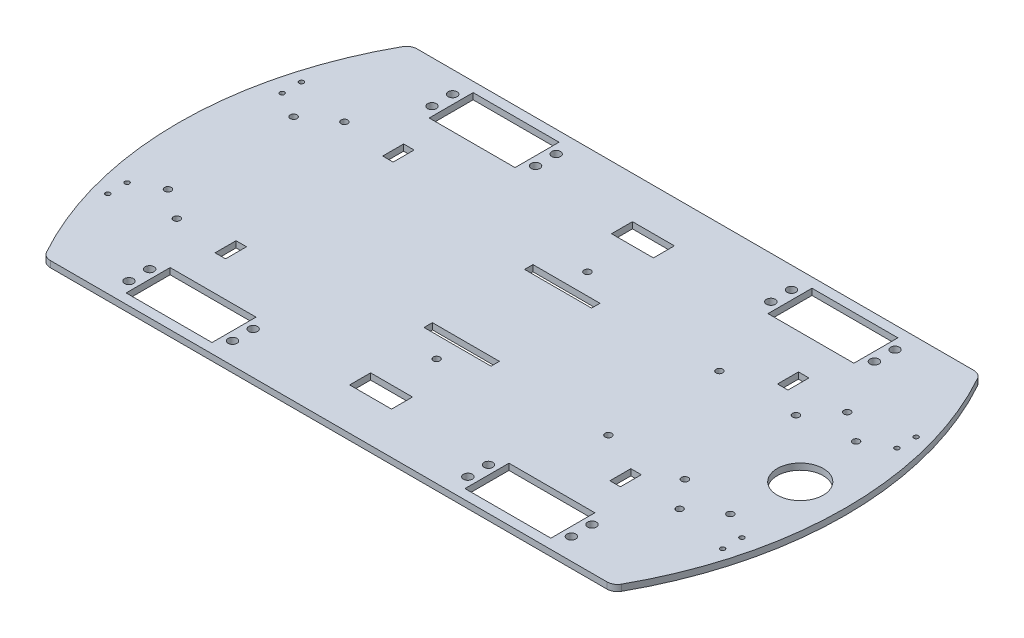
SolidWorks part; units mm, degrees
material "Acrylic (Medium-high impact)"
ref_plane "Front Plane" through (0, 0, 0) normal (0, 0, 1) x (1, 0, 0)
ref_plane "Top Plane" through (0, 0, 0) normal (0, 1, 0) x (1, 0, 0)
ref_plane "Right Plane" through (0, 0, 0) normal (1, 0, 0) x (0, 0, -1)
sketch "Sketch1" plane through (0, 0, 0) normal (0, 1, 0) x (1, 0, 0)
  line L1 (-150, -87.5) -> (150, -87.5) construction
  line L2 (-150, -87.5) -> (-150, 87.5) construction
  line L3 (-150, 87.5) -> (150, 87.5) construction
  line L4 (150, -87.5) -> (150, 87.5) construction
  line L5 (-150, -87.5) -> (150, 87.5) construction
  line L6 (-150, 87.5) -> (150, -87.5) construction
  line L7 (-94.037, 37.4826) -> (-29.037, 37.4826) construction
  line L12 (-150, 0) -> (150, 0) construction
  line L13 (-126.5544, 87.5) -> (-104.0544, 87.5)
  line L19 (-89.087, -10.5) -> (-48.087, 10.5) construction
  line L20 (-89.087, 10.5) -> (-48.087, -10.5) construction
  line L24 (-94.037, -37.4826) -> (-29.037, -37.4826) construction
  line L26 (-61.537, 37.4826) -> (-61.537, -37.4826) construction
  line L27 (-68.587, 10.5) -> (-68.587, -10.5) construction
  line L45 (80, 57.5) -> (80, -57.5) construction
  line L47 (40.8363, 87.5) -> (-18.2182, 87.5)
  line L67 (-126.5544, -87.5) -> (-104.0544, -87.5)
  line L78 (40.8363, -87.5) -> (-18.2182, -87.5)
  line L79 (120.8363, -87.5) -> (137.7923, -87.5)
  line L80 (120.8363, 87.5) -> (137.7923, 87.5)
  line L81 (54.4, -34.9) -> (64.4, -37.9) construction
  line L82 (54.4, 37.9) -> (64.4, 37.9) construction
  line L83 (54.4, 37.9) -> (54.4, 34.9) construction
  line L84 (54.4, 34.9) -> (64.4, 34.9) construction
  line L85 (64.4, 37.9) -> (64.4, 34.9) construction
  line L86 (54.4, 37.9) -> (64.4, 34.9) construction
  line L87 (54.4, 34.9) -> (64.4, 37.9) construction
  line L88 (54.4, -37.9) -> (64.4, -34.9) construction
  line L89 (64.4, -37.9) -> (64.4, -34.9) construction
  line L90 (54.4, -34.9) -> (64.4, -34.9) construction
  line L91 (54.4, -37.9) -> (54.4, -34.9) construction
  line L92 (54.4, -37.9) -> (64.4, -37.9) construction
  line L93 (0, 87.5) -> (0, -87.5) construction
  line L94 (-6.77, -22) -> (25.23, -26) construction
  line L95 (127.5, -12.5) -> (137.5, -12.5) construction
  line L96 (127.5, -12.5) -> (127.5, 12.5) construction
  line L97 (127.5, 12.5) -> (137.5, 12.5) construction
  line L98 (137.5, -12.5) -> (137.5, 12.5) construction
  line L99 (127.5, -12.5) -> (137.5, 12.5) construction
  line L100 (127.5, 12.5) -> (137.5, -12.5) construction
  line L101 (-6.77, 22) -> (25.23, 22)
  line L102 (-6.77, 22) -> (-6.77, 26)
  line L103 (-6.77, 26) -> (25.23, 26)
  line L104 (25.23, 22) -> (25.23, 26)
  line L105 (-6.77, 22) -> (25.23, 26) construction
  line L106 (-6.77, 26) -> (25.23, 22) construction
  line L107 (-6.77, -26) -> (25.23, -22) construction
  line L108 (-6.77, -26) -> (25.23, -26)
  line L109 (25.23, -22) -> (25.23, -26)
  line L110 (-6.77, -22) -> (25.23, -22)
  line L111 (-6.77, -22) -> (-6.77, -26)
  line L112 (-0.77, -67.5) -> (19.23, -57.5) construction
  line L117 (-0.77, 57.5) -> (19.23, 57.5)
  line L118 (-0.77, 57.5) -> (-0.77, 67.5)
  line L119 (-0.77, 67.5) -> (19.23, 67.5)
  line L124 (19.23, 57.5) -> (19.23, 67.5)
  line L125 (-0.77, 57.5) -> (19.23, 67.5) construction
  line L126 (-0.77, 67.5) -> (19.23, 57.5) construction
  line L127 (-0.77, -57.5) -> (19.23, -67.5) construction
  line L128 (-0.77, -67.5) -> (19.23, -67.5)
  line L129 (19.23, -57.5) -> (19.23, -67.5)
  line L130 (-0.77, -57.5) -> (19.23, -57.5)
  line L131 (-0.77, -57.5) -> (-0.77, -67.5)
  line L132 (-104.0544, -87.5) -> (-18.2182, -87.5)
  line L133 (-127.5, -5) -> (-122.5, -5) construction
  line L134 (-127.5, -5) -> (-127.5, 5) construction
  line L135 (-127.5, 5) -> (-122.5, 5) construction
  line L136 (-122.5, -5) -> (-122.5, 5) construction
  line L137 (-127.5, -5) -> (-122.5, 5) construction
  line L138 (-127.5, 5) -> (-122.5, -5) construction
  line L140 (-104.0544, 87.5) -> (-18.2182, 87.5)
  line L141 (40.8363, -87.5) -> (120.8363, -87.5)
  line L142 (40.8363, 87.5) -> (120.8363, 87.5)
  line L143 (-61.537, -72.32) -> (-39.9764, -72.32) construction
  line L144 (80, -72.32) -> (50.3837, -72.32) construction
  line L145 (9.23, 98.8163) -> (9.23, -100.4279) construction
  line L146 (137.7923, 87.5) -> (145.0144, 87.5)
  line L147 (137.7923, -87.5) -> (145.0144, -87.5)
  line L148 (69.6, 82.82) -> (110.6, 82.82)
  line L149 (-71.937, -61.82) -> (-30.937, -61.82) construction
  line L150 (-71.937, -61.82) -> (-71.937, -82.82) construction
  line L151 (-71.937, -82.82) -> (-30.937, -82.82) construction
  line L152 (-30.937, -61.82) -> (-30.937, -82.82) construction
  line L153 (69.6, -61.82) -> (110.6, -61.82)
  line L154 (69.6, -61.82) -> (69.6, -82.82)
  line L155 (69.6, -82.82) -> (110.6, -82.82)
  line L156 (110.6, -61.82) -> (110.6, -82.82)
  line L157 (110.6, 61.82) -> (110.6, 82.82)
  line L158 (69.6, 61.82) -> (110.6, 61.82)
  line L159 (69.6, 61.82) -> (69.6, 82.82)
  line L160 (-71.937, 61.82) -> (-30.937, 61.82) construction
  line L161 (-30.937, 61.82) -> (-30.937, 82.82) construction
  line L162 (-71.937, 82.82) -> (-30.937, 82.82) construction
  line L163 (-71.937, 61.82) -> (-71.937, 82.82) construction
  line L164 (4.23, 35.4) -> (4.23, -35.9) construction
  line L165 (-120.7635, 13.4) -> (-39.9764, 13.4) construction
  line L166 (71.9375, 13.4) -> (158.7021, 13.4) construction
  line L167 (-363.8153, 13.4) -> (-363.8153, -13.4) construction
  line L168 (-363.8153, -13.4) -> (-440.2138, -13.4) construction
  line L169 (-440.2138, -13.4) -> (-440.2138, -35.4) construction
  line L170 (-440.2138, -35.4) -> (-480.6138, 5) construction
  line L171 (-480.6138, 5) -> (-440.2138, 45.4) construction
  line L172 (-440.2138, 45.4) -> (-440.2138, 13.4) construction
  line L173 (-440.2138, 13.4) -> (-363.8153, 13.4) construction
  line L174 (-92.137, 61.82) -> (-92.137, 82.82)
  line L175 (-92.137, -61.82) -> (-51.137, -61.82)
  line L176 (-92.137, -61.82) -> (-92.137, -82.82)
  line L177 (-92.137, -82.82) -> (-51.137, -82.82)
  line L178 (-51.137, -61.82) -> (-51.137, -82.82)
  line L179 (-92.137, 61.82) -> (-51.137, 61.82)
  line L180 (-92.137, 82.82) -> (-51.137, 82.82)
  line L181 (-51.137, 61.82) -> (-51.137, 82.82)
  line L182 (-82.5, 45) -> (-87.5, 45)
  line L183 (-82.5, -45) -> (-87.5, -45)
  line L184 (-82.5, -45) -> (-82.5, -35)
  line L185 (-82.5, -35) -> (-87.5, -35)
  line L186 (-87.5, -45) -> (-87.5, -35)
  line L187 (-82.5, -45) -> (-87.5, -35) construction
  line L188 (-82.5, -35) -> (-87.5, -45) construction
  line L189 (-82.5, 45) -> (-82.5, 35)
  line L190 (-82.5, 35) -> (-87.5, 35)
  line L191 (-87.5, 45) -> (-87.5, 35)
  line L192 (100.96, 35) -> (105.96, 35)
  line L193 (100.96, 45) -> (100.96, 35)
  line L194 (100.96, 45) -> (105.96, 45)
  line L195 (105.96, 45) -> (105.96, 35)
  line L196 (100.96, -45) -> (105.96, -45)
  line L197 (100.96, -45) -> (100.96, -35)
  line L198 (100.96, -35) -> (105.96, -35)
  line L199 (105.96, -45) -> (105.96, -35)
  line L201 (118.25, -26.5) -> (81.75, -26.5) construction
  line L202 (118.25, -26.5) -> (118.25, 26.5) construction
  line L203 (118.25, 26.5) -> (81.75, 26.5) construction
  line L204 (81.75, -26.5) -> (81.75, 26.5) construction
  line L205 (118.25, -26.5) -> (81.75, 26.5) construction
  line L206 (118.25, 26.5) -> (81.75, -26.5) construction
  arc A7 (-126.5544, 87.5) -> (-126.5544, -87.5) centre (25, 0) ccw
  circle A11 centre (-110.77, 40) radius 1.6
  circle A14 centre (-110.77, -40) radius 1.6
  circle A15 centre (-125, -30) radius 1.6
  circle A16 centre (9.23, -36) radius 1.6
  circle A17 centre (143.46, -30) radius 1.6
  circle A18 centre (143.46, 30) radius 1.6
  circle A19 centre (9.23, 36) radius 1.6
  circle A20 centre (-125, 30) radius 1.6
  circle A21 centre (-137.5, 37) radius 1.1
  circle A29 centre (-137.5, 46.2) radius 1.1
  circle A31 centre (-137.5, -37) radius 1.1
  circle A32 centre (-137.5, -46.2) radius 1.1
  circle A37 centre (-76.147, -77.245) radius 2.1 construction
  circle A38 centre (-76.147, -67.395) radius 2.1 construction
  circle A39 centre (-26.7247, -77.245) radius 2.1 construction
  circle A40 centre (-26.7247, -67.395) radius 2.1 construction
  circle A41 centre (-26.7247, 67.395) radius 2.1 construction
  circle A42 centre (-26.7247, 77.245) radius 2.1 construction
  circle A43 centre (-76.147, 67.395) radius 2.1 construction
  circle A44 centre (-76.147, 77.245) radius 2.1 construction
  circle A45 centre (65.39, -77.245) radius 2.1
  circle A46 centre (65.39, -67.395) radius 2.1
  circle A47 centre (114.8123, -77.245) radius 2.1
  circle A48 centre (114.8123, -67.395) radius 2.1
  circle A49 centre (114.8123, 67.395) radius 2.1
  circle A50 centre (114.8123, 77.245) radius 2.1
  circle A51 centre (65.39, 67.395) radius 2.1
  circle A52 centre (65.39, 77.245) radius 2.1
  arc A53 (145.0144, 87.5) -> (145.0144, -87.5) centre (-6.54, 0) cw
  circle A54 centre (155.96, 37) radius 1.1
  circle A55 centre (155.96, 46.2) radius 1.1
  circle A56 centre (155.96, -46.2) radius 1.1
  circle A57 centre (155.96, -37) radius 1.1
  circle A58 centre (-118.8, 13.4) radius 1.1 construction
  circle A59 centre (-60, 13.4) radius 1.1 construction
  circle A62 centre (-60, -13.4) radius 1.1 construction
  circle A63 centre (-118.8, -13.4) radius 1.1 construction
  circle A64 centre (94.66, 13.4) radius 1.1 construction
  circle A65 centre (153.46, 13.4) radius 1.1 construction
  circle A66 centre (153.46, -13.4) radius 1.1 construction
  circle A67 centre (94.66, -13.4) radius 1.1 construction
  circle A68 centre (-46.927, -67.395) radius 2.1
  circle A69 centre (-46.927, -77.245) radius 2.1
  circle A70 centre (-96.3493, -67.395) radius 2.1
  circle A71 centre (-96.3493, -77.245) radius 2.1
  circle A72 centre (-96.3493, 77.245) radius 2.1
  circle A73 centre (-96.3493, 67.395) radius 2.1
  circle A74 centre (-46.927, 77.245) radius 2.1
  circle A75 centre (-46.927, 67.395) radius 2.1
  circle A76 centre (129.23, 40) radius 1.6
  circle A77 centre (129.23, -40) radius 1.6
  circle A78 centre (-105, 0) radius 2.1 construction
  circle A79 centre (81.75, 26.5) radius 1.6
  circle A80 centre (146.828, 0) radius 11
  circle A81 centre (118.25, 26.5) radius 1.6
  circle A82 centre (81.75, -26.5) radius 1.6
  circle A83 centre (118.25, -26.5) radius 1.6
  point P0 (0, 0)
  point P18 (-68.587, 0)
  point P53 (59.4, 36.4)
  point P79 (59.4, -36.4)
  point P101 (9.23, 24)
  point P103 (132.5, 0)
  point P111 (9.23, -24)
  point P116 (9.23, 62.5)
  point P127 (9.23, -62.5)
  point P134 (-125, 0)
  point P145 (80, -72.32)
  point P153 (-61.537, -72.32)
  point P154 (80, 72.32)
  point P155 (-61.537, 72.32)
  point P197 (168.46, 0)
  point P237 (-85, -40)
  point P248 (100, 0)
  dimension "D15" = 21
  dimension "D19" = 9.85
  dimension "D21" = 20.6
  dimension "D23" = 40
  dimension "D24" = 175
  dimension "D26" = 240
  dimension "D28" = 4.21
  dimension "D34" = 5
  dimension "D22" = 3.2
  dimension "D27" = 3.2
  dimension "D41" = 3.2
  dimension "D43" = 3.2
  dimension "D50" = 20
  dimension "D51" = 10
  dimension "D54" = 2.2
  dimension "D60" = 2.2
  dimension "D61" = 2.2
  dimension "D7" = 4.2
  dimension "D18" = 4.2
  dimension "D70" = 2.2
  dimension "D73" = 14.61
  dimension "D75" = 4.2
  dimension "D80" = 4.2
  dimension "D85" = 22
  dimension "D86" = 3.2
  dimension "D1" = 175
  dimension "D2" = 300
  dimension "D8" = 9.85
  dimension "D9" = 22.5
  dimension "D10" = 9.85
  dimension "D11" = 49.4223
  dimension "D12" = 41
  dimension "D13" = 21
  dimension "D14" = 9.23
  dimension "D16" = 41
  dimension "D17" = 14.61
  dimension "D20" = 49.4223
  dimension "D25" = 14.61
  dimension "D29" = 10.5
  dimension "D30" = 21
  dimension "D31" = 41
  dimension "D32" = 10.5
  dimension "D33" = 4.21
  dimension "D35" = 10
  dimension "D36" = 3
  dimension "D37" = 13.4
  dimension "D38" = 125
  dimension "D39" = 143.46
  dimension "D40" = 10
  dimension "D42" = 25
  dimension "D44" = 30
  dimension "D45" = 132.5
  dimension "D46" = 4
  dimension "D47" = 32
  dimension "D48" = 24
  dimension "D49" = 10
  dimension "D52" = 58.8
  dimension "D53" = 25
  dimension "D55" = 37
  dimension "D56" = 12.5
  dimension "D57" = 5
  dimension "D58" = 10
  dimension "D59" = 25
  dimension "D62" = 9.2
  dimension "D63" = 80
  dimension "D64" = 72.32
  dimension "D65" = 72.32
  dimension "D66" = 61.537
  dimension "D67" = 60
  dimension "D68" = 13.4
  dimension "D69" = 58.8
  dimension "D71" = 15
  dimension "D72" = 41
  dimension "D74" = 4.21
  dimension "D76" = 49.4223
  dimension "D77" = 5
  dimension "D78" = 40
  dimension "D79" = 85
  dimension "D81" = 105
  dimension "D82" = 36
  dimension "D83" = 53
  dimension "D84" = 36.5
  dimension "D87" = 100
extrude "Boss-Extrude1" add sketch "Sketch1" along normal blind 3
fillet "Fillet1" radius 5 4 edges at (-126.5544, 1.5, 87.5) (145.0144, 1.5, 87.5) (145.0144, 1.5, -87.5) (-126.5544, 1.5, -87.5)
